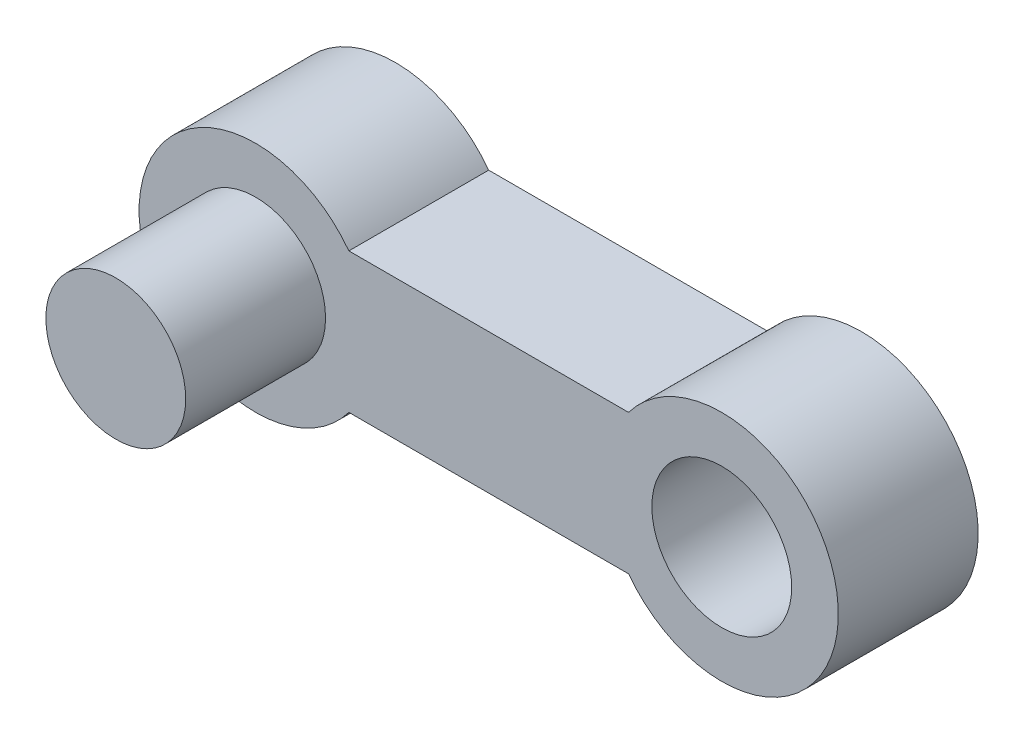
SolidWorks part; units mm, degrees
ref_plane "Спереди" through (0, 0, 0) normal (0, 0, 1) x (1, 0, 0)
ref_plane "Сверху" through (0, 0, 0) normal (0, 1, 0) x (1, 0, 0)
ref_plane "Справа" through (0, 0, 0) normal (1, 0, 0) x (0, 0, -1)
other "Configuration Table"
sketch "Sketch2" plane through (0, 0, 0) normal (0, 0, 1) x (1, 0, 0)
  line L0 (-21.8667, 8.413) -> (-21.8667, 18.8078) construction
  line L1 (-25.8667, 14.9242) -> (-17.8667, 14.9242)
  line L2 (-25.8667, 14.9242) -> (-25.8667, 11.9242)
  line L3 (-25.8667, 11.9242) -> (-17.8667, 11.9242)
  line L4 (-17.8667, 14.9242) -> (-17.8667, 11.9242)
  line L5 (-25.8667, 14.9242) -> (-17.8667, 11.9242) construction
  line L6 (-25.8667, 11.9242) -> (-17.8667, 14.9242) construction
  line L7 (-16.9512, 13.4242) -> (-39.3291, 13.4242) construction
  circle A0 centre (-26.8667, 13.4242) radius 2.5
  circle A2 centre (-16.8667, 13.4242) radius 2.5
  point P0 (-21.8667, 13.4242)
  point P13 (-39.1168, 10.4335)
  point P14 (-40.0435, 12.4242)
  dimension "D3" = 5
  dimension "D1" = 8
  dimension "D2" = 3
  dimension "D4" = 5
extrude "Boss-Extrude1" add sketch "Sketch2" along normal blind 3 contours L1 A0 L3 L2 | L3 A2 L1 A0 | A2 L1 L4 L3
ref_plane "Plane1" through (0, 0, 3) normal (0, 0, 1) x (1, 0, 0)
sketch "Sketch3" plane through (0, 0, 3) normal (0, 0, 1) x (1, 0, 0)
  circle A0 centre (-26.8667, 13.4242) radius 1.5
  dimension "D1" = 3
extrude "Boss-Extrude2" add sketch "Sketch3" along normal blind 3
ref_plane "Plane2" through (0, 0, 0) normal (0, 0, -1) x (-1, 0, 0)
sketch "Sketch4" plane through (0, 0, 0) normal (0, 0, -1) x (-1, 0, 0)
  circle A0 centre (16.8667, 13.4242) radius 1.5
  circle A1 centre (26.8667, 13.4242) radius 1.5 construction
extrude "Cut-Extrude1" cut sketch "Sketch4" against normal up to surface (3 mm away) up to face at (-25.3667, 13.4242, 3)
